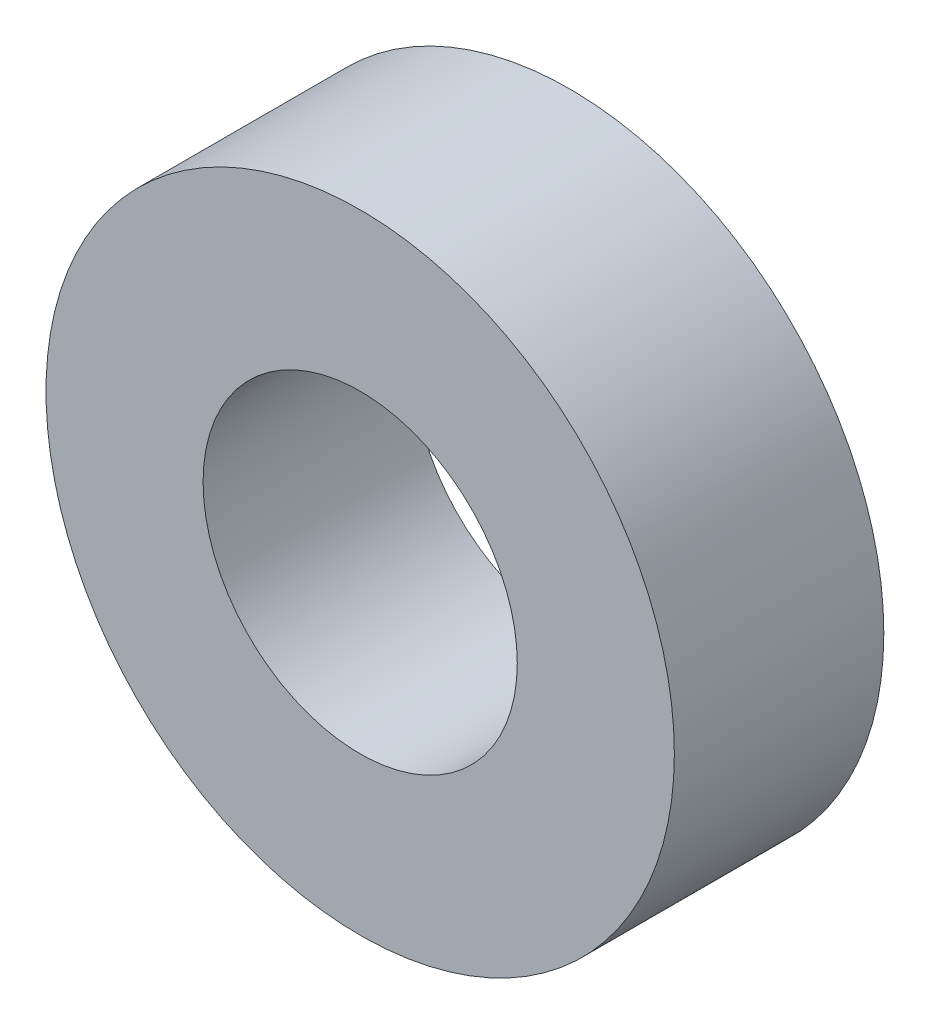
SolidWorks part; units mm, degrees
ref_plane "前视基准面" through (0, 0, 0) normal (0, 0, 1) x (1, 0, 0)
ref_plane "上视基准面" through (0, 0, 0) normal (0, 1, 0) x (1, 0, 0)
ref_plane "右视基准面" through (0, 0, 0) normal (1, 0, 0) x (0, 0, -1)
sketch "草图1" plane through (0, 0, 0) normal (0, 0, 1) x (1, 0, 0)
  circle A0 centre (0, 0.8318) radius 6
  circle A1 centre (0, 0.8318) radius 3
extrude "凸台-拉伸1" add sketch "草图1" along normal blind 4
